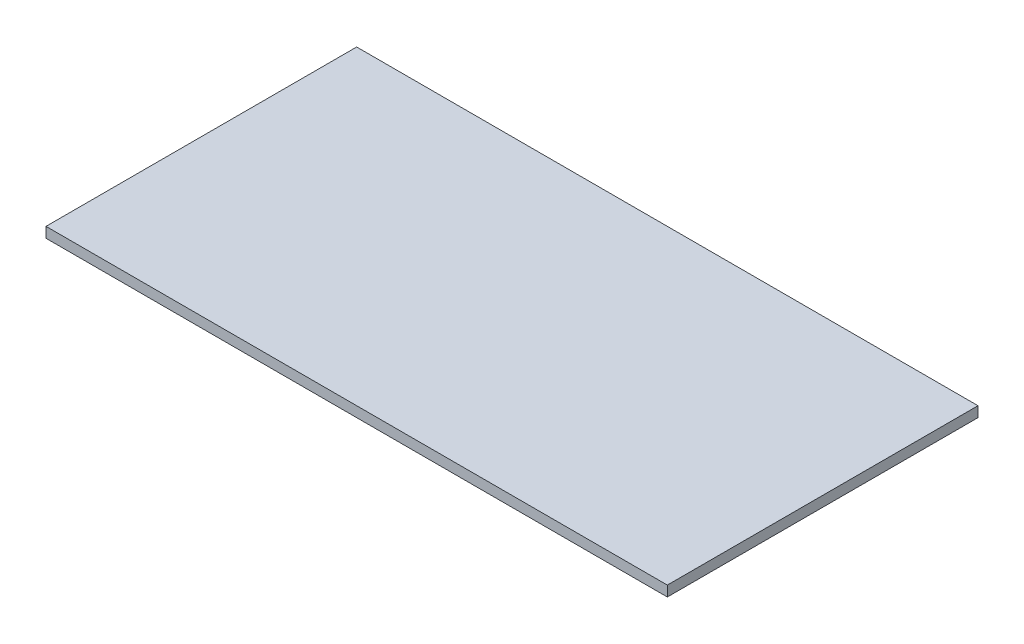
SolidWorks part; units mm, degrees
ref_plane "Front Plane" through (0, 0, 0) normal (0, 0, 1) x (1, 0, 0)
ref_plane "Top Plane" through (0, 0, 0) normal (0, 1, 0) x (1, 0, 0)
ref_plane "Right Plane" through (0, 0, 0) normal (1, 0, 0) x (0, 0, -1)
sketch "Sketch1" plane through (0, 0, 0) normal (0, 1, 0) x (1, 0, 0)
  line L1 (300, -150) -> (-300, -150)
  line L2 (300, -150) -> (300, 150)
  line L3 (300, 150) -> (-300, 150)
  line L4 (-300, -150) -> (-300, 150)
  line L5 (300, -150) -> (-300, 150) construction
  line L6 (300, 150) -> (-300, -150) construction
  point P0 (0, 0)
extrude "Boss-Extrude1" add sketch "Sketch1" along normal blind 10
